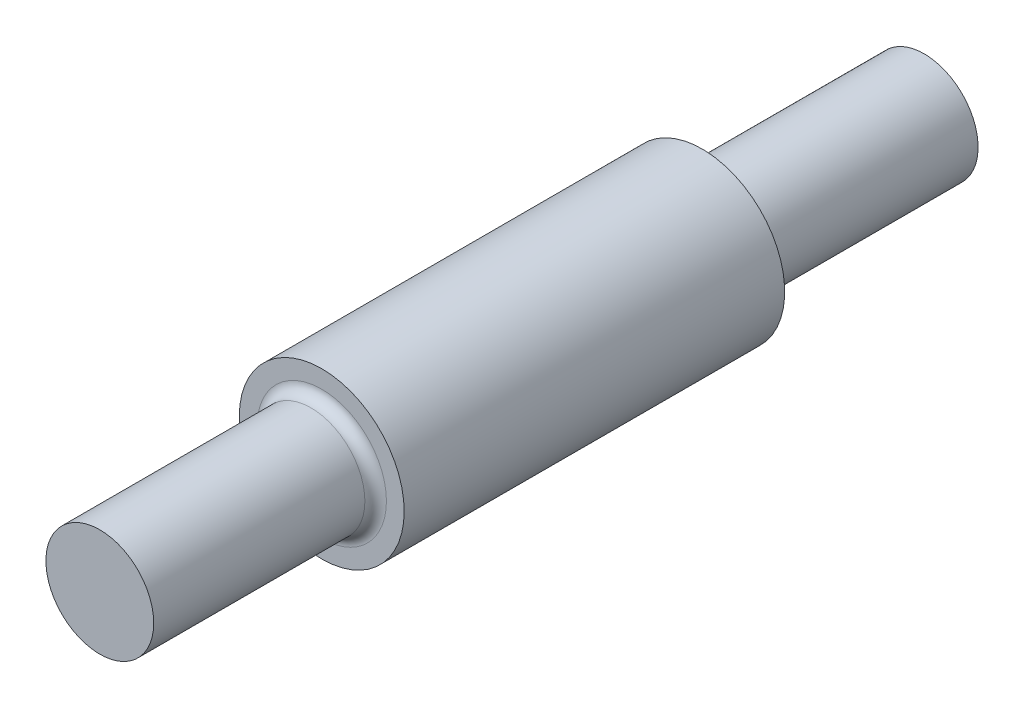
SolidWorks part; units mm, degrees
ref_plane "Front Plane" through (0, 0, 0) normal (0, 0, 1) x (1, 0, 0)
ref_plane "Top Plane" through (0, 0, 0) normal (0, 1, 0) x (1, 0, 0)
ref_plane "Right Plane" through (0, 0, 0) normal (1, 0, 0) x (0, 0, -1)
sketch "Sketch2" plane through (0, 0, 0) normal (0, 0, 1) x (1, 0, 0)
  circle A0 centre (0, 0) radius 13
  dimension "D1" = 26
extrude "Boss-Extrude1" add sketch "Sketch2" along normal blind 130
sketch "Sketch3" plane through (0, 0, 130) normal (0, 0, 1) x (1, 0, 0)
  circle A0 centre (0, 0) radius 8.5
  circle A1 centre (0, 0) radius 13
  dimension "D1" = 17
  dimension "D2" = 26
extrude "Cut-Extrude1" cut sketch "Sketch3" against normal blind 35
sketch "Sketch4" plane through (0, 0, 0) normal (0, 0, -1) x (-1, 0, 0)
  circle A0 centre (0, 0) radius 8.5
  circle A1 centre (0, 0) radius 13
  dimension "D1" = 17
  dimension "D2" = 26
extrude "Cut-Extrude2" cut sketch "Sketch4" against normal blind 35
fillet "Fillet1" radius 1.7 1 edges at (8.5, 0, 95)
fillet "Fillet2" radius 1.7 1 edges at (-8.5, 0, 35)
